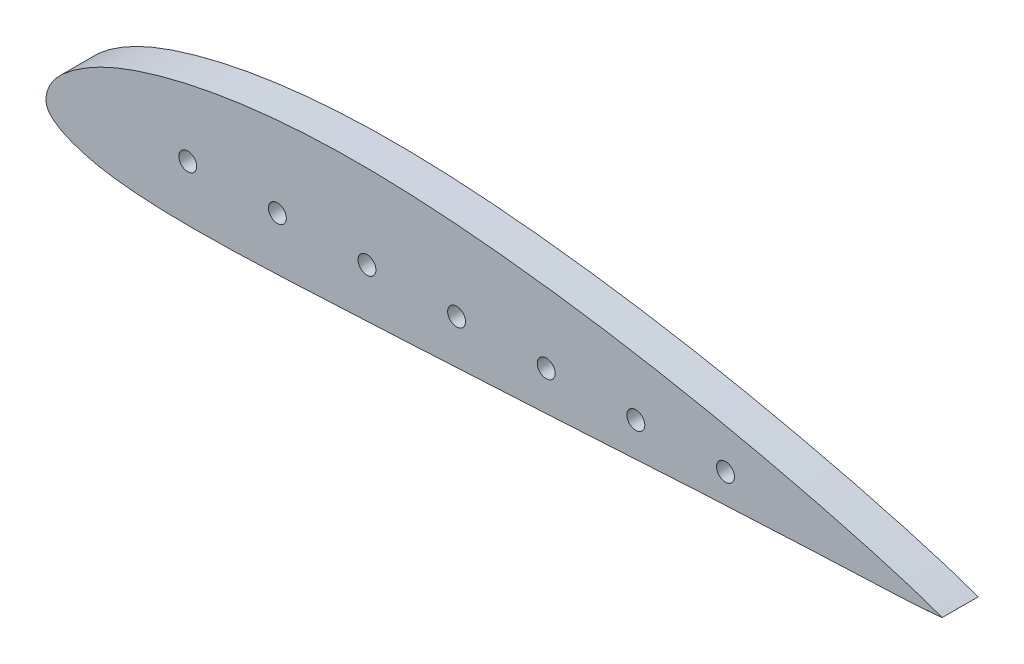
SolidWorks part; units mm, degrees
ref_plane "Front Plane" through (0, 0, 0) normal (0, 0, 1) x (1, 0, 0)
ref_plane "Top Plane" through (0, 0, 0) normal (0, 1, 0) x (1, 0, 0)
ref_plane "Right Plane" through (0, 0, 0) normal (1, 0, 0) x (0, 0, -1)
curve "Curve6"
  spline degree 3 poles (25.3425, -0.0032, 0) (25.4146, -0.0017, 0) (25.3409, 0.0182, 0) (25.2821, 0.0451, 0) (25.1344, 0.0958, 0) (24.9517, 0.161, 0) (24.709, 0.2432, 0) (24.4175, 0.3367, 0) (24.0747, 0.4415, 0) (23.6834, 0.5551, 0) (23.2451, 0.6783, 0) (22.7618, 0.81, 0) (22.2354, 0.9484, 0) (21.6681, 1.0919, 0) (21.0623, 1.2389, 0) (20.4209, 1.3885, 0) (19.7464, 1.5394, 0) (19.0417, 1.6901, 0) (18.3099, 1.8386, 0) (17.5539, 1.9826, 0) (16.7773, 2.1212, 0) (15.9832, 2.2523, 0) (15.1749, 2.3749, 0) (14.3561, 2.4876, 0) (13.5301, 2.589, 0) (12.7007, 2.6789, 0) (11.8712, 2.7549, 0) (11.0452, 2.8159, 0) (10.2263, 2.8599, 0) (9.4178, 2.885, 0) (8.6235, 2.8892, 0) (7.8465, 2.8727, 0) (7.0902, 2.8342, 0) (6.3579, 2.774, 0) (5.6528, 2.6933, 0) (4.9779, 2.5936, 0) (4.3359, 2.4765, 0) (3.7299, 2.3419, 0) (3.1621, 2.1931, 0) (2.6348, 2.0323, 0) (2.15, 1.859, 0) (1.7108, 1.6713, 0) (1.3186, 1.4721, 0) (0.9759, 1.2652, 0) (0.6817, 1.0585, 0) (0.4381, 0.8519, 0) (0.2437, 0.6447, 0) (0.1056, 0.4314, 0) (0.023, 0.2224, 0) (-0.0092, 0.0288, 0) (0.0156, -0.1458, 0) (0.1079, -0.2922, 0) (0.2518, -0.4161, 0) (0.4427, -0.535, 0) (0.6865, -0.6448, 0) (0.9795, -0.749, 0) (1.3229, -0.8412, 0) (1.7153, -0.9161, 0) (2.1543, -0.9744, 0) (2.6382, -1.0177, 0) (3.165, -1.046, 0) (3.7325, -1.0605, 0) (4.3383, -1.0625, 0) (4.9798, -1.0547, 0) (5.6544, -1.0368, 0) (6.3592, -1.0098, 0) (7.0911, -0.9767, 0) (7.8469, -0.9396, 0) (8.6236, -0.9006, 0) (9.4177, -0.8609, 0) (10.2259, -0.8201, 0) (11.0447, -0.7781, 0) (11.8706, -0.7345, 0) (12.7, -0.6894, 0) (13.5294, -0.6427, 0) (14.3553, -0.5946, 0) (15.1742, -0.5462, 0) (15.9823, -0.4975, 0) (16.7764, -0.4501, 0) (17.5531, -0.4056, 0) (18.3089, -0.3633, 0) (19.0409, -0.3246, 0) (19.7457, -0.2888, 0) (20.4202, -0.2559, 0) (21.0617, -0.2255, 0) (21.6674, -0.1973, 0) (22.2347, -0.1717, 0) (22.7612, -0.1486, 0) (23.2445, -0.1279, 0) (23.6828, -0.1103, 0) (24.074, -0.0935, 0) (24.4169, -0.0769, 0) (24.7085, -0.0595, 0) (24.9513, -0.0416, 0) (25.1346, -0.0248, 0) (25.2812, -0.0133, 0) (25.3425, -0.0032, 0) (25.4146, -0.0017, 0) (25.3409, 0.0182, 0) knots -0.004677 -0.002084 -0.000521 0 0.000552 0.002207 0.004953 0.008769 0.013624 0.019492 0.026331 0.034118 0.042815 0.05238 0.06278 0.073959 0.085865 0.098446 0.111647 0.125415 0.139681 0.154378 0.169447 0.184821 0.200433 0.216224 0.232117 0.248051 0.26396 0.279777 0.295442 0.310885 0.326054 0.340892 0.355349 0.369378 0.38293 0.395953 0.40841 0.420261 0.431467 0.441988 0.451799 0.46091 0.469304 0.476946 0.483798 0.489858 0.495198 0.499997 0.504304 0.507974 0.511123 0.514149 0.51765 0.521912 0.526982 0.532916 0.539692 0.547309 0.555757 0.565025 0.575098 0.58594 0.597509 0.609762 0.622649 0.636122 0.650118 0.664572 0.679425 0.694613 0.710068 0.725733 0.741529 0.757395 0.773262 0.789063 0.804734 0.820197 0.835393 0.850252 0.864712 0.878713 0.892194 0.905092 0.917358 0.92894 0.939788 0.949856 0.959093 0.967472 0.974955 0.981503 0.987099 0.99171 0.995323 0.997916 0.999479 1 1.000552 1.002207 1.004953 periodic
sketch "Sketch1" plane through (0, 0, 0) normal (0, 0, 1) x (1, 0, 0)
  spline S0 degree 3 poles (109.1641, -5.0959) (109.5248, -5.0884) (109.1565, -4.9889) (108.8625, -4.8546) (108.1239, -4.6012) (107.2103, -4.2751) (105.997, -3.8641) (104.5392, -3.3964) (102.8253, -2.8727) (100.8686, -2.3043) (98.6771, -1.6887) (96.2608, -1.0302) (93.6288, -0.3381) (90.7922, 0.3794) (87.7635, 1.1143) (84.5564, 1.8623) (81.1839, 2.617) (77.6605, 3.3705) (74.0011, 4.113) (70.2214, 4.8329) (66.3384, 5.5261) (62.3678, 6.1816) (58.3265, 6.7947) (54.2323, 7.3581) (50.1023, 7.8652) (45.9552, 8.3145) (41.8079, 8.6946) (37.6778, 8.9994) (33.5831, 9.2196) (29.5409, 9.3448) (25.5691, 9.3662) (21.6843, 9.2836) (17.903, 9.0908) (14.2414, 8.7901) (10.7158, 8.3865) (7.3413, 7.8879) (4.1315, 7.3023) (1.1013, 6.6295) (-1.7375, 5.8853) (-4.3742, 5.0814) (-6.798, 4.2151) (-8.9943, 3.2766) (-10.9551, 2.2806) (-12.6686, 1.2462) (-14.1399, 0.2127) (-15.3577, -0.8207) (-16.3296, -1.8567) (-17.0203, -2.9228) (-17.4333, -3.9681) (-17.5941, -4.9361) (-17.4702, -5.8089) (-17.0087, -6.5411) (-16.2891, -7.1605) (-15.3347, -7.7551) (-14.1159, -8.3042) (-12.6509, -8.8251) (-10.9336, -9.2859) (-8.9717, -9.6604) (-6.7766, -9.952) (-4.3574, -10.1687) (-1.7234, -10.3101) (1.1144, -10.3827) (4.1435, -10.3926) (7.351, -10.3534) (10.7239, -10.2642) (14.2476, -10.1292) (17.9072, -9.9637) (21.6864, -9.7779) (25.5696, -9.5832) (29.5401, -9.3844) (33.5812, -9.1805) (37.6754, -8.9705) (41.805, -8.7523) (45.952, -8.5268) (50.099, -8.2935) (54.2285, -8.0531) (58.3226, -7.8111) (62.3635, -7.5677) (66.3338, -7.3306) (70.2171, -7.1081) (73.9965, -6.8963) (77.6563, -6.7028) (81.1802, -6.5242) (84.5529, -6.3594) (87.7601, -6.2077) (90.7886, -6.0665) (93.6254, -5.9384) (96.2577, -5.8231) (98.6745, -5.7196) (100.8659, -5.6315) (102.8219, -5.5477) (104.5361, -5.4647) (105.9942, -5.3773) (107.2081, -5.2879) (108.1248, -5.204) (108.8576, -5.1465) (109.1641, -5.0959) (109.5248, -5.0884) (109.1565, -4.9889) knots -0.004677 -0.002084 -0.000521 0 0.000552 0.002207 0.004953 0.008769 0.013624 0.019492 0.026331 0.034118 0.042815 0.05238 0.06278 0.073959 0.085865 0.098446 0.111647 0.125415 0.139681 0.154378 0.169447 0.184821 0.200433 0.216224 0.232117 0.248051 0.26396 0.279777 0.295442 0.310885 0.326054 0.340892 0.355349 0.369378 0.38293 0.395953 0.40841 0.420261 0.431467 0.441988 0.451799 0.46091 0.469304 0.476946 0.483798 0.489858 0.495198 0.499997 0.504304 0.507974 0.511123 0.514149 0.51765 0.521912 0.526982 0.532916 0.539692 0.547309 0.555757 0.565025 0.575098 0.58594 0.597509 0.609762 0.622649 0.636122 0.650118 0.664572 0.679425 0.694613 0.710068 0.725733 0.741529 0.757395 0.773262 0.789063 0.804734 0.820197 0.835393 0.850252 0.864712 0.878713 0.892194 0.905092 0.917358 0.92894 0.939788 0.949856 0.959093 0.967472 0.974955 0.981503 0.987099 0.99171 0.995323 0.997916 0.999479 1 1.000552 1.002207 1.004953 only from (109.4518, -5.08) to (109.4518, -5.08)
  spline S1 degree 3 poles (25.3425, -0.0032) (25.4146, -0.0017) (25.3409, 0.0182) (25.2821, 0.0451) (25.1344, 0.0958) (24.9517, 0.161) (24.709, 0.2432) (24.4175, 0.3367) (24.0747, 0.4415) (23.6834, 0.5551) (23.2451, 0.6783) (22.7618, 0.81) (22.2354, 0.9484) (21.6681, 1.0919) (21.0623, 1.2389) (20.4209, 1.3885) (19.7464, 1.5394) (19.0417, 1.6901) (18.3099, 1.8386) (17.5539, 1.9826) (16.7773, 2.1212) (15.9832, 2.2523) (15.1749, 2.3749) (14.3561, 2.4876) (13.5301, 2.589) (12.7007, 2.6789) (11.8712, 2.7549) (11.0452, 2.8159) (10.2263, 2.8599) (9.4178, 2.885) (8.6235, 2.8892) (7.8465, 2.8727) (7.0902, 2.8342) (6.3579, 2.774) (5.6528, 2.6933) (4.9779, 2.5936) (4.3359, 2.4765) (3.7299, 2.3419) (3.1621, 2.1931) (2.6348, 2.0323) (2.15, 1.859) (1.7108, 1.6713) (1.3186, 1.4721) (0.9759, 1.2652) (0.6817, 1.0585) (0.4381, 0.8519) (0.2437, 0.6447) (0.1056, 0.4314) (0.023, 0.2224) (-0.0092, 0.0288) (0.0156, -0.1458) (0.1079, -0.2922) (0.2518, -0.4161) (0.4427, -0.535) (0.6865, -0.6448) (0.9795, -0.749) (1.3229, -0.8412) (1.7153, -0.9161) (2.1543, -0.9744) (2.6382, -1.0177) (3.165, -1.046) (3.7325, -1.0605) (4.3383, -1.0625) (4.9798, -1.0547) (5.6544, -1.0368) (6.3592, -1.0098) (7.0911, -0.9767) (7.8469, -0.9396) (8.6236, -0.9006) (9.4177, -0.8609) (10.2259, -0.8201) (11.0447, -0.7781) (11.8706, -0.7345) (12.7, -0.6894) (13.5294, -0.6427) (14.3553, -0.5946) (15.1742, -0.5462) (15.9823, -0.4975) (16.7764, -0.4501) (17.5531, -0.4056) (18.3089, -0.3633) (19.0409, -0.3246) (19.7457, -0.2888) (20.4202, -0.2559) (21.0617, -0.2255) (21.6674, -0.1973) (22.2347, -0.1717) (22.7612, -0.1486) (23.2445, -0.1279) (23.6828, -0.1103) (24.074, -0.0935) (24.4169, -0.0769) (24.7085, -0.0595) (24.9513, -0.0416) (25.1346, -0.0248) (25.2812, -0.0133) (25.3425, -0.0032) (25.4146, -0.0017) (25.3409, 0.0182) knots -0.004677 -0.002084 -0.000521 0 0.000552 0.002207 0.004953 0.008769 0.013624 0.019492 0.026331 0.034118 0.042815 0.05238 0.06278 0.073959 0.085865 0.098446 0.111647 0.125415 0.139681 0.154378 0.169447 0.184821 0.200433 0.216224 0.232117 0.248051 0.26396 0.279777 0.295442 0.310885 0.326054 0.340892 0.355349 0.369378 0.38293 0.395953 0.40841 0.420261 0.431467 0.441988 0.451799 0.46091 0.469304 0.476946 0.483798 0.489858 0.495198 0.499997 0.504304 0.507974 0.511123 0.514149 0.51765 0.521912 0.526982 0.532916 0.539692 0.547309 0.555757 0.565025 0.575098 0.58594 0.597509 0.609762 0.622649 0.636122 0.650118 0.664572 0.679425 0.694613 0.710068 0.725733 0.741529 0.757395 0.773262 0.789063 0.804734 0.820197 0.835393 0.850252 0.864712 0.878713 0.892194 0.905092 0.917358 0.92894 0.939788 0.949856 0.959093 0.967472 0.974955 0.981503 0.987099 0.99171 0.995323 0.997916 0.999479 1 1.000552 1.002207 1.004953 only from (25.4, 0) to (25.4, 0) construction
  spline S2 degree 3 poles (25.3425, -0.0032) (25.4146, -0.0017) (25.3409, 0.0182) (25.2821, 0.0451) (25.1344, 0.0958) (24.9517, 0.161) (24.709, 0.2432) (24.4175, 0.3367) (24.0747, 0.4415) (23.6834, 0.5551) (23.2451, 0.6783) (22.7618, 0.81) (22.2354, 0.9484) (21.6681, 1.0919) (21.0623, 1.2389) (20.4209, 1.3885) (19.7464, 1.5394) (19.0417, 1.6901) (18.3099, 1.8386) (17.5539, 1.9826) (16.7773, 2.1212) (15.9832, 2.2523) (15.1749, 2.3749) (14.3561, 2.4876) (13.5301, 2.589) (12.7007, 2.6789) (11.8712, 2.7549) (11.0452, 2.8159) (10.2263, 2.8599) (9.4178, 2.885) (8.6235, 2.8892) (7.8465, 2.8727) (7.0902, 2.8342) (6.3579, 2.774) (5.6528, 2.6933) (4.9779, 2.5936) (4.3359, 2.4765) (3.7299, 2.3419) (3.1621, 2.1931) (2.6348, 2.0323) (2.15, 1.859) (1.7108, 1.6713) (1.3186, 1.4721) (0.9759, 1.2652) (0.6817, 1.0585) (0.4381, 0.8519) (0.2437, 0.6447) (0.1056, 0.4314) (0.023, 0.2224) (-0.0092, 0.0288) (0.0156, -0.1458) (0.1079, -0.2922) (0.2518, -0.4161) (0.4427, -0.535) (0.6865, -0.6448) (0.9795, -0.749) (1.3229, -0.8412) (1.7153, -0.9161) (2.1543, -0.9744) (2.6382, -1.0177) (3.165, -1.046) (3.7325, -1.0605) (4.3383, -1.0625) (4.9798, -1.0547) (5.6544, -1.0368) (6.3592, -1.0098) (7.0911, -0.9767) (7.8469, -0.9396) (8.6236, -0.9006) (9.4177, -0.8609) (10.2259, -0.8201) (11.0447, -0.7781) (11.8706, -0.7345) (12.7, -0.6894) (13.5294, -0.6427) (14.3553, -0.5946) (15.1742, -0.5462) (15.9823, -0.4975) (16.7764, -0.4501) (17.5531, -0.4056) (18.3089, -0.3633) (19.0409, -0.3246) (19.7457, -0.2888) (20.4202, -0.2559) (21.0617, -0.2255) (21.6674, -0.1973) (22.2347, -0.1717) (22.7612, -0.1486) (23.2445, -0.1279) (23.6828, -0.1103) (24.074, -0.0935) (24.4169, -0.0769) (24.7085, -0.0595) (24.9513, -0.0416) (25.1346, -0.0248) (25.2812, -0.0133) (25.3425, -0.0032) (25.4146, -0.0017) (25.3409, 0.0182) knots -0.004677 -0.002084 -0.000521 0 0.000552 0.002207 0.004953 0.008769 0.013624 0.019492 0.026331 0.034118 0.042815 0.05238 0.06278 0.073959 0.085865 0.098446 0.111647 0.125415 0.139681 0.154378 0.169447 0.184821 0.200433 0.216224 0.232117 0.248051 0.26396 0.279777 0.295442 0.310885 0.326054 0.340892 0.355349 0.369378 0.38293 0.395953 0.40841 0.420261 0.431467 0.441988 0.451799 0.46091 0.469304 0.476946 0.483798 0.489858 0.495198 0.499997 0.504304 0.507974 0.511123 0.514149 0.51765 0.521912 0.526982 0.532916 0.539692 0.547309 0.555757 0.565025 0.575098 0.58594 0.597509 0.609762 0.622649 0.636122 0.650118 0.664572 0.679425 0.694613 0.710068 0.725733 0.741529 0.757395 0.773262 0.789063 0.804734 0.820197 0.835393 0.850252 0.864712 0.878713 0.892194 0.905092 0.917358 0.92894 0.939788 0.949856 0.959093 0.967472 0.974955 0.981503 0.987099 0.99171 0.995323 0.997916 0.999479 1 1.000552 1.002207 1.004953 only from (25.4, 0) to (25.4, 0) construction
  dimension "D1" = 109.4518
  dimension "D2" = 5.08
extrude "Boss-Extrude1" add sketch "Sketch1" along normal blind 5.08
sketch "Sketch3" plane through (0, 0, 5.08) normal (0, 0, 1) x (1, 0, 0)
  circle A0 centre (2.54, -2.54) radius 1.27
  circle A1 centre (15.24, -2.54) radius 1.27
  circle A2 centre (27.94, -2.54) radius 1.27
  circle A3 centre (53.34, -2.54) radius 1.27
  circle A4 centre (78.74, -2.54) radius 1.27
  circle A5 centre (40.64, -2.54) radius 1.27
  circle A6 centre (66.04, -2.54) radius 1.27
  point P13 (0, 0)
  dimension "D1" = 2.54
  dimension "D2" = 2.54
  dimension "D8" = 12.7
  dimension "D3" = 12.7
  dimension "D4" = 12.7
  dimension "D5" = 25.4
  dimension "D6" = 25.4
  dimension "D7" = 2.54
  dimension "D9" = 12.7
extrude "Cut-Extrude1" cut sketch "Sketch3" against normal up to surface (5.08 mm away)
